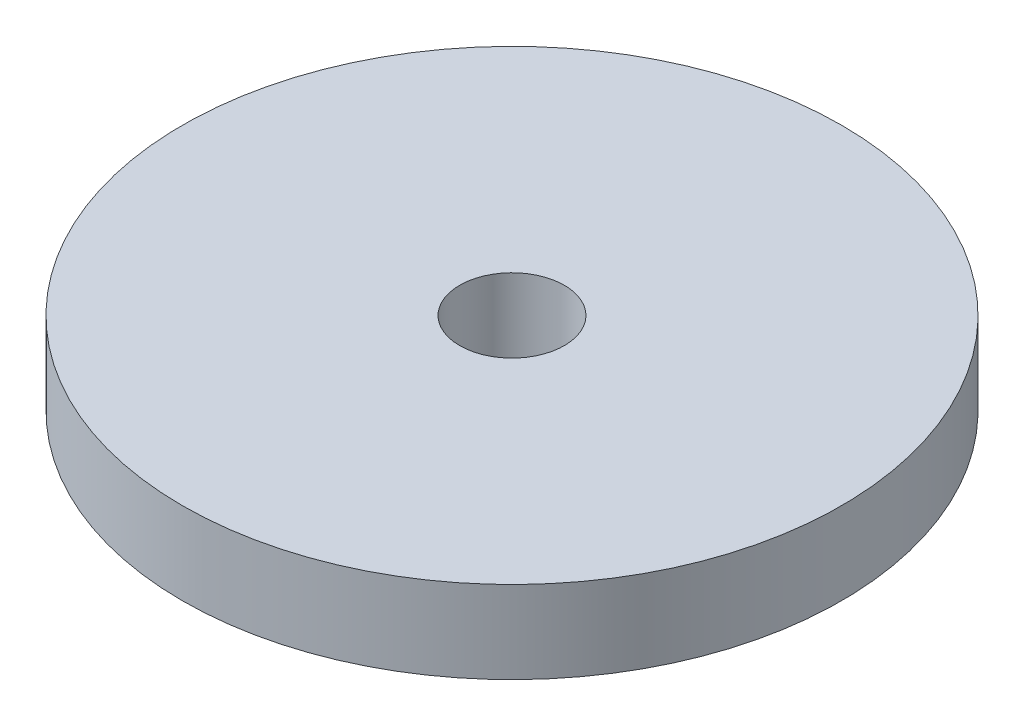
SolidWorks part; units mm, degrees
ref_plane "Plan de face" through (0, 0, 0) normal (0, 0, 1) x (1, 0, 0)
ref_plane "Plan de dessus" through (0, 0, 0) normal (0, 1, 0) x (1, 0, 0)
ref_plane "Plan de droite" through (0, 0, 0) normal (1, 0, 0) x (0, 0, -1)
sketch "Esquisse2" plane through (0, 0, 0) normal (0, 1, 0) x (1, 0, 0)
  circle A0 centre (-7.2415, 12.136) radius 3.175
  circle A1 centre (-7.2415, 12.136) radius 20
extrude "Boss.-Extru.1" add sketch "Esquisse2" along normal blind 5
